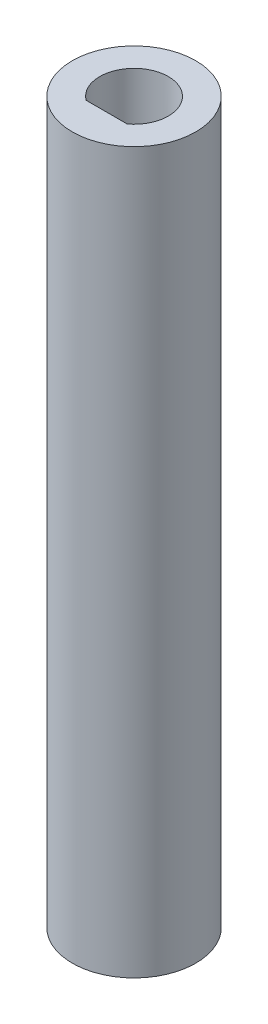
SolidWorks part; units mm, degrees
ref_plane "Front Plane" through (0, 0, 0) normal (0, 0, 1) x (1, 0, 0)
ref_plane "Top Plane" through (0, 0, 0) normal (0, 1, 0) x (1, 0, 0)
ref_plane "Right Plane" through (0, 0, 0) normal (1, 0, 0) x (0, 0, -1)
sketch "Sketch1" plane through (0, 0, 0) normal (0, 1, 0) x (1, 0, 0)
  line L0 (0, 0) -> (0, -3.175) construction
  line L1 (0, 0) -> (3.175, 0) construction
  line L2 (0, -2.54) -> (1.905, -2.54) construction
  line L3 (1.905, -2.54) -> (-1.905, -2.54)
  circle A0 centre (0, 0) radius 3.175 construction
  arc A1 (1.905, -2.54) -> (-1.905, -2.54) centre (0, 0) ccw
  circle A2 centre (0, 0) radius 5.715
  dimension "D1" = 6.35
  dimension "D3" = 11.43
  dimension "D2" = 0.635
extrude "Boss-Extrude1" add sketch "Sketch1" along normal blind 12.7
sketch "Sketch3" plane through (0, 0, 0) normal (0, -1, 0) x (-1, 0, 0)
  circle A0 centre (0, 0) radius 5.715
extrude "Boss-Extrude2" add sketch "Sketch3" along normal blind 53.975
sketch "Sketch4" plane through (0, -53.975, 0) normal (0, -1, 0) x (1, 0, 0)
  line L0 (0, 2.54) -> (-1.7961, 4.3361)
  line L1 (-2.54, -2.54) -> (2.54, -2.54) construction
  line L2 (-2.54, -2.54) -> (-2.54, 2.54) construction
  line L3 (-2.54, 2.54) -> (2.54, 2.54) construction
  line L4 (2.54, -2.54) -> (2.54, 2.54) construction
  line L5 (-2.54, -2.54) -> (2.54, 2.54) construction
  line L6 (-2.54, 2.54) -> (2.54, -2.54) construction
  line L7 (-2.54, 0) -> (-4.3361, 1.7961)
  line L8 (-4.3361, 1.7961) -> (-1.7961, 4.3361)
  line L9 (2.54, 0) -> (4.3361, -1.7961)
  line L10 (0, -2.54) -> (1.7961, -4.3361)
  line L11 (1.7961, -4.3361) -> (4.3361, -1.7961)
  line L12 (-2.54, 0) -> (-4.3361, -1.7961)
  line L13 (0, -2.54) -> (-1.7961, -4.3361)
  line L14 (-4.3361, -1.7961) -> (-1.7961, -4.3361)
  line L15 (2.54, 0) -> (4.3361, 1.7961)
  line L16 (1.7961, 4.3361) -> (4.3361, 1.7961)
  line L17 (0, 2.54) -> (1.7961, 4.3361)
  point P0 (0, 0)
  dimension "D1" = 2.54
  dimension "D2" = 5.08
  dimension "D3" = 5.08
  dimension "D4" = 8.6721
  dimension "D5" = 3.5921
  dimension "D6" = 3.5921
  dimension "D7" = 3.5921
  dimension "D8" = 3.5921
  dimension "D9" = 8.6721
  dimension "D10" = 0
  dimension "D11" = 3.5921
  dimension "D12" = 5.08
  dimension "D13" = 2.54
  dimension "D14" = 2.54
  dimension "D15" = 2.54
  dimension "D16" = 2.54
  dimension "D17" = 2.54
  dimension "D18" = 2.54
  dimension "D19" = 2.54
  dimension "D20" = 2.54
extrude "Cut-Extrude1" cut sketch "Sketch4" against normal blind 53.975
